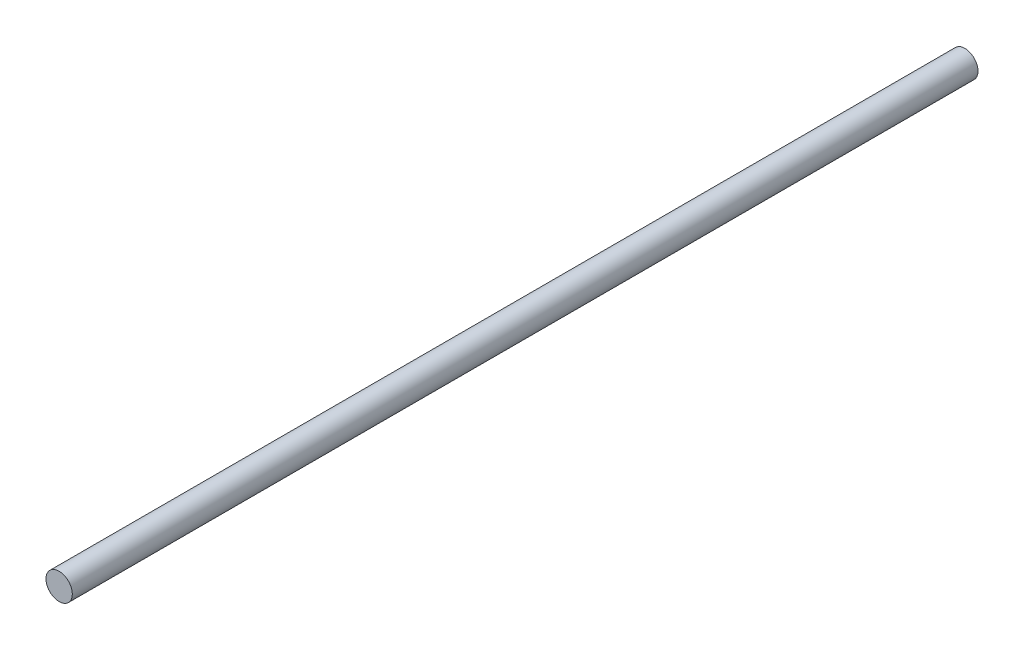
SolidWorks part; units mm, degrees
ref_plane "Front Plane" through (0, 0, 0) normal (0, 0, 1) x (1, 0, 0)
ref_plane "Top Plane" through (0, 0, 0) normal (0, 1, 0) x (1, 0, 0)
ref_plane "Right Plane" through (0, 0, 0) normal (1, 0, 0) x (0, 0, -1)
sketch "Sketch1" plane through (0, 0, 0) normal (0, 0, 1) x (1, 0, 0)
  circle A0 centre (0, 0) radius 5
extrude "Boss-Extrude1" add sketch "Sketch1" along normal blind 344
